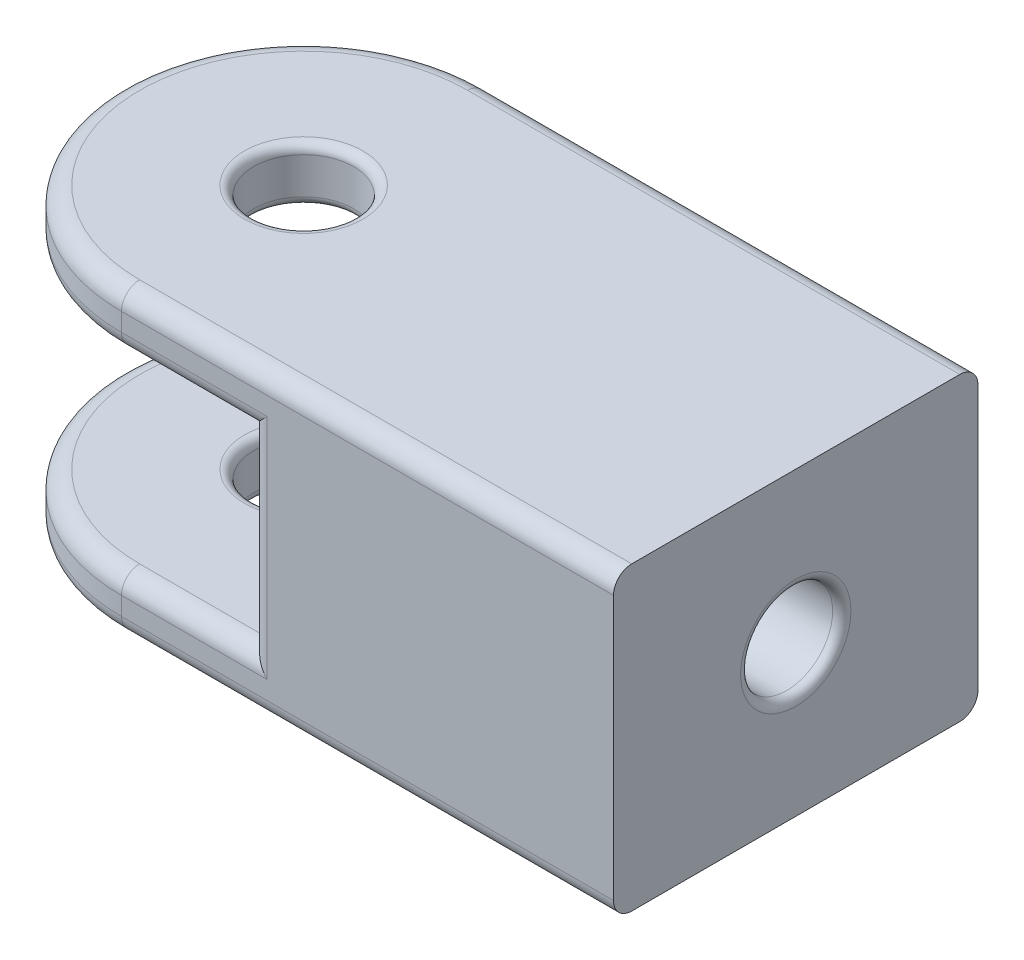
SolidWorks part; units mm, degrees
ref_plane "Front Plane" through (0, 0, 0) normal (0, 0, 1) x (1, 0, 0)
ref_plane "Top Plane" through (0, 0, 0) normal (0, 1, 0) x (1, 0, 0)
ref_plane "Right Plane" through (0, 0, 0) normal (1, 0, 0) x (0, 0, -1)
sketch "Sketch2" plane through (0, 0, 0) normal (0, 1, 0) x (1, 0, 0)
  line L0 (0, 10) -> (10, 10)
  line L1 (10, 10) -> (10, -10)
  line L2 (10, -10) -> (0, -10)
  arc A0 (0, 10) -> (0, -10) centre (0, 0) ccw
  circle A1 centre (0, 0) radius 2.75
  dimension "D1" = 20
  dimension "D2" = 5.5
  dimension "D3" = 10
extrude "Boss-Extrude1" add sketch "Sketch2" against normal blind 3
sketch "Sketch3" plane through (10, 0, 0) normal (1, 0, 0) x (0, 0, -1)
  line L0 (10, -3) -> (10, 0) construction
  line L5 (-10, 0) -> (10, 0)
  line L6 (-10, 0) -> (-10, -13.5)
  line L7 (-10, -13.5) -> (10, -13.5)
  line L8 (10, 0) -> (10, -13.5)
  line L9 (-10, 0) -> (10, -13.5) construction
  line L10 (-10, -13.5) -> (10, 0) construction
  line L11 (-10, -3) -> (10, -3) construction
  point P4 (0, -6.75)
  dimension "D1" = 10.5
extrude "Boss-Extrude2" add sketch "Sketch3" against normal blind 3
sketch "Sketch4" plane through (0, -13.5, 0) normal (0, -1, 0) x (1, 0, 0)
  line L3 (0, -10) -> (10, -10)
  line L4 (10, 10) -> (0, 10)
  line L5 (10, -10) -> (10, 10)
  line L6 (0, -10) -> (10, -10)
  line L7 (10, 10) -> (0, 10)
  line L8 (10, -10) -> (10, 10)
  circle A1 centre (0, 0) radius 2.75
  circle A2 centre (0, 0) radius 2.75
  arc A3 (0, 10) -> (0, -10) centre (0, 0) ccw
  arc A4 (0, 10) -> (0, -10) centre (0, 0) ccw
  dimension "D1" = 0
  dimension "D2" = 0
extrude "Boss-Extrude3" add sketch "Sketch4" along normal blind 3
sketch "Sketch5" plane through (10, 0, 0) normal (1, 0, 0) x (0, 0, -1)
  line L4 (10, 0) -> (-10, 0)
  line L5 (-10, 0) -> (-10, -16.5)
  line L6 (-10, -16.5) -> (10, -16.5)
  line L7 (10, -16.5) -> (10, 0)
  line L8 (10, 0) -> (-10, 0)
  line L9 (-10, 0) -> (-10, -16.5)
  line L10 (-10, -16.5) -> (10, -16.5)
  line L11 (10, -16.5) -> (10, 0)
  dimension "D1" = 0
extrude "Boss-Extrude4" add sketch "Sketch5" along normal blind 17
sketch "Sketch6" plane through (27, 0, 0) normal (1, 0, 0) x (0, 0, -1)
  circle A0 centre (0, -8.25) radius 2.525
  dimension "D1" = 5.05
extrude "Cut-Extrude1" cut sketch "Sketch6" against normal offset from surface (17 mm away) 3 up to face at (7, -8.25, 0)
fillet "Fillet1" radius 1 14 edges at (7, -8.25, -10) (7, -8.25, 10) (-10, -13.5, 0) (3.5, -13.5, -10) (3.5, -13.5, 10) (3.5, -3, -10) (-10, -3, 0) (3.5, -3, 10) (-10, -16.5, 0) (13.5, -16.5, 10) (13.5, -16.5, -10) (13.5, 0, 10) (-10, 0, 0) (13.5, 0, -10)
fillet "Fillet2" radius 0.5 6 edges at (0, -13.5, -2.75) (0, -16.5, -2.75) (0, -3, 2.75) (0, 0, 2.75) (27, -8.25, -2.525) (10, -8.25, -2.525)
